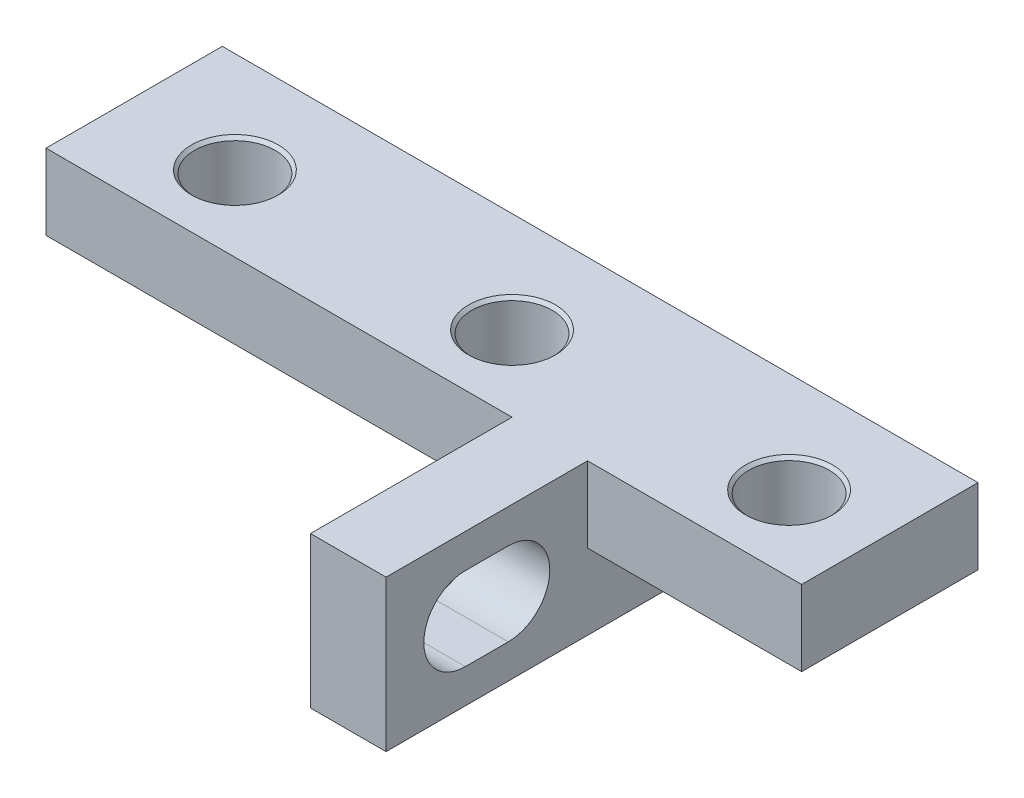
SolidWorks part; units mm, degrees
ref_plane "Front" through (0, 0, 0) normal (0, 0, 1) x (1, 0, 0)
ref_plane "Top" through (0, 0, 0) normal (0, 1, 0) x (1, 0, 0)
ref_plane "Right" through (0, 0, 0) normal (1, 0, 0) x (0, 0, -1)
sketch "Эскиз1" plane through (0, 0, 0) normal (0, 0, 1) x (1, 0, 0)
  line L0 (-1.5, 0) -> (-1.5, 22)
  line L1 (-1.5, 22) -> (-20, 22)
  line L2 (-20, 22) -> (-20, 25)
  line L3 (-20, 25) -> (20, 25)
  line L4 (20, 25) -> (20, 22)
  line L5 (20, 22) -> (1.5, 22)
  line L6 (1.5, 22) -> (1.5, 0)
  line L7 (1.5, 0) -> (-1.5, 0)
  line L8 (0, 0) -> (0, 25) construction
  dimension "D1" = 3
  dimension "D2" = 3
  dimension "D3" = 40
  dimension "D4" = 25
extrude "Бобышка-Вытянуть1" add sketch "Эскиз1" along normal blind 15
sketch "Эскиз2" plane through (0, 0, 15) normal (0, 0, 1) x (1, 0, 0)
  line L0 (20, 25) -> (-20, 25) construction
  line L1 (-20, 19) -> (10, 19)
  line L2 (-20, 19) -> (-20, 25)
  line L3 (-20, 25) -> (10, 25)
  line L4 (10, 19) -> (10, 25)
  line L5 (-20, 19) -> (10, 25) construction
  line L6 (-20, 25) -> (10, 19) construction
  line L8 (-20, 25) -> (-20, 22) construction
  point P0 (-5, 22)
  line M1 (-1.5, 0) -> (1.5, 0)
  line M2 (1.5, 0) -> (1.5, 22)
  line M3 (1.5, 22) -> (20, 22)
  line M4 (20, 22) -> (20, 25)
  line M5 (20, 25) -> (-20, 25)
  line M8 (-1.5, 22) -> (-1.5, 0)
  dimension "D1" = 30
  dimension "D2" = 6
extrude "Вырез-Вытянуть1" cut sketch "Эскиз2" against normal through all contours L1 M8 M1 M2 | L4 M3 M4 M5
sketch "Эскиз3" plane through (0, 0, 15) normal (0, 0, 1) x (1, 0, 0)
  line L0 (-1.5, 22) -> (-1.5, 25)
  line L1 (10, 25) -> (-20, 25) construction
  line L2 (1.5, 22) -> (1.5, 25)
extrude "Вырез-Вытянуть3" cut sketch "Эскиз3" against normal offset from surface (8 mm away) 7 up to face at (-2.5, 22, 0)
hole_wizard "Отверстие с зазором M31" positions "Эскиз5" profile "Эскиз4" hole size "M3" standard "DIN" end condition through all
sketch "Эскиз5" plane through (0, 22, 0) normal (0, -1, 0) x (1, 0, 0)
  line L3 (10, 0) -> (10, 7) construction
  line L4 (-20, 7) -> (-1.5, 7) construction
  point P0 (-15.5, 4)
  point P1 (6.5, 4)
  point P14 (-4.5, 4)
  dimension "D1" = 22
  dimension "D2" = 3
  dimension "D3" = 3.5
  dimension "D4" = 11
sketch "Эскиз4" plane through (-15.5, 22, 4) normal (1, 0, 0) x (0, 0, -1)
  line L0 (0, 0) -> (0, 3)
  line L1 (0, 3) -> (1.725, 3)
  line L2 (1.6, 2.875) -> (1.6, 0.125)
  line L3 (1.6, 0.125) -> (1.725, 0)
  line L5 (1.725, 0) -> (0, 0)
  line L6 (-1.6, 0.125) -> (-1.725, 0) construction
  line L7 (1.725, 3) -> (1.6, 2.875)
  line L8 (-1.725, 3) -> (-1.6, 2.875) construction
  line L11 (0, -6.35) -> (0, 107.95) construction
  dimension "Диаметр сквозного отверстия" = 3.2
  dimension "Глубина сквозного отверстия" = 3
  dimension "Диаметр передней зенковки" = 3.45
  dimension "Угол передней зенковки" = 90
  dimension "Диаметр задней зенковки" = 3.45
  dimension "Угол задней зенковки" = 90
sketch "Эскиз6" plane through (1.5, 0, 0) normal (1, 0, 0) x (0, 0, -1)
  line L0 (-11.85, 22) -> (-10.15, 22) construction
  line L1 (-11.85, 23.65) -> (-10.15, 23.65)
  line L2 (-11.85, 20.35) -> (-10.15, 20.35)
  line L3 (-7, 22) -> (-7, 25) construction
  line L4 (-8.5, 22) -> (-8.5, 19) construction
  line L5 (0, 19) -> (-15, 19) construction
  line L6 (-7, 25) -> (-15, 25) construction
  arc A0 (-11.85, 23.65) -> (-11.85, 20.35) centre (-11.85, 22) ccw
  arc A1 (-10.15, 20.35) -> (-10.15, 23.65) centre (-10.15, 22) ccw
  point P2 (-11, 22)
  dimension "D1" = 3.3
  dimension "D2" = 5
  dimension "D3" = 3
  dimension "D4" = 1.5
extrude "Вырез-Вытянуть4" cut sketch "Эскиз6" against normal up to next
